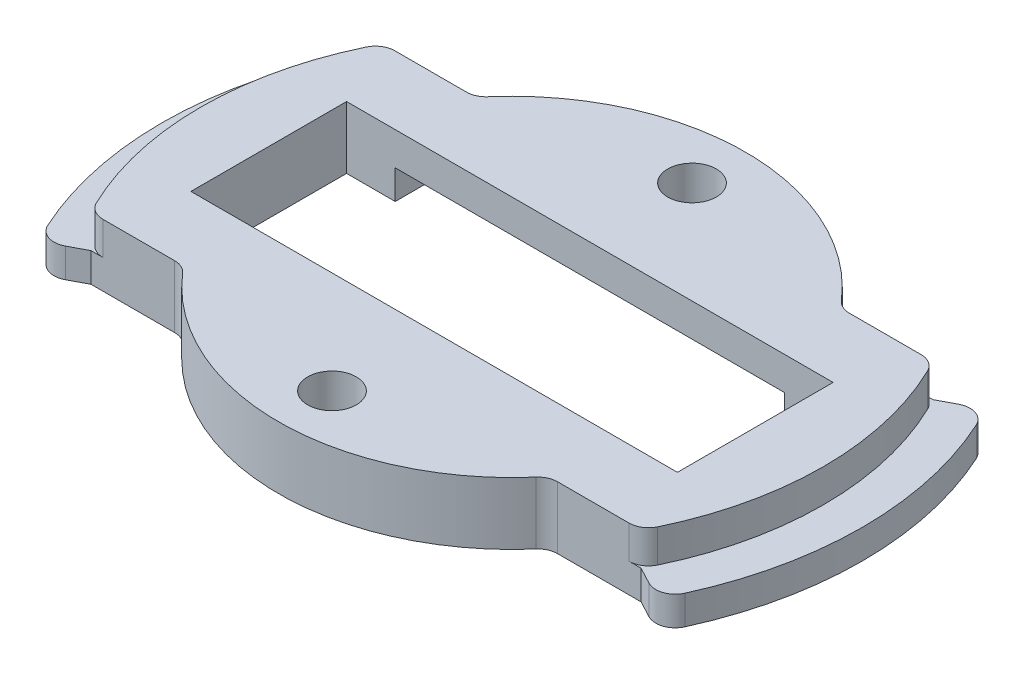
SolidWorks part; units mm, degrees
material "ABS"
ref_plane "Front Plane" through (0, 0, 0) normal (0, 0, 1) x (1, 0, 0)
ref_plane "Top Plane" through (0, 0, 0) normal (0, 1, 0) x (1, 0, 0)
ref_plane "Right Plane" through (0, 0, 0) normal (1, 0, 0) x (0, 0, -1)
sketch "Sketch1" plane through (0, 0, 0) normal (0, 1, 0) x (1, 0, 0)
  line L0 (0, 0) -> (0, 8) construction
  line L1 (0, 0) -> (20, 0) construction
  line L2 (-20, 8) -> (20, 8)
  line L3 (-20, 8) -> (-20, -8)
  line L4 (-20, -8) -> (20, -8)
  line L5 (20, 8) -> (20, -8)
  line L6 (28.2666, 15) -> (-28.2666, 15)
  line L7 (28.2666, -15) -> (-28.2666, -15)
  line L8 (-25, 15) -> (-25, -15) construction
  line L9 (-28.2666, 15) -> (-28.2666, -15) construction
  arc A0 (-28.2666, 15) -> (-28.2666, -15) centre (0, 0) ccw
  arc A1 (28.2666, 15) -> (28.2666, -15) centre (0, 0) cw
  point P10 (0, 15)
  point P17 (0, -15)
  dimension "D4" = 5
  dimension "D5" = 32
  dimension "D1" = 40
  dimension "D2" = 16
  dimension "D3" = 15
extrude "Boss-Extrude1" add sketch "Sketch1" along normal blind 6.4
sketch "Sketch2" plane through (0, 0, 0) normal (0, -1, 0) x (1, 0, 0)
  line L0 (-20, 0) -> (20, 0) construction
  line L1 (-20, 8) -> (20, 8)
  line L2 (-20, 8) -> (-20, 12)
  line L3 (-20, 12) -> (20, 12)
  line L4 (20, 8) -> (20, 12)
  line L5 (-20, -8) -> (-20, 8) construction
  line L6 (20, 8) -> (20, -8) construction
  line L7 (20, -8) -> (20, -12)
  line L8 (-20, -12) -> (20, -12)
  line L9 (-20, -8) -> (-20, -12)
  line L10 (-20, -8) -> (20, -8)
  dimension "D1" = 4
extrude "Cut-Extrude1" cut sketch "Sketch2" against normal blind 3
sketch "Sketch3" plane through (0, 0, 0) normal (0, -1, 0) x (1, 0, 0)
  line L0 (0, 12) -> (0, -12) construction
  line L1 (20, 12) -> (-20, 12) construction
  line L2 (-20, -12) -> (20, -12) construction
  line L3 (-20, -12) -> (-20, 12) construction
  line L4 (-20, 8) -> (-25, 8)
  line L5 (-20, 8) -> (-20, -8)
  line L6 (-20, -8) -> (-25, -8)
  line L7 (-25, 8) -> (-25, -8)
  line L8 (-20, 8) -> (20, 8) construction
  line L9 (20, -8) -> (-20, -8) construction
  line L10 (25, 8) -> (25, -8)
  line L11 (20, -8) -> (25, -8)
  line L12 (20, 8) -> (20, -8)
  line L13 (20, 8) -> (25, 8)
  dimension "D1" = 5
extrude "Cut-Extrude2" cut sketch "Sketch3" against normal through all
sketch "Sketch5" plane through (0, 6.4, 0) normal (0, 1, 0) x (1, 0, 0)
  line L0 (-28.2666, -15) -> (28.2666, -15) construction
  line L1 (-18.735, -15) -> (18.735, -15)
  line L2 (-25, 0) -> (25, 0) construction
  line L3 (-25, -8) -> (-25, 8) construction
  line L4 (25, 8) -> (25, -8) construction
  line L5 (-18.735, 15) -> (18.735, 15)
  arc A0 (-18.735, -15) -> (18.735, -15) centre (0, 0) ccw
  arc A1 (-18.735, 15) -> (18.735, 15) centre (0, 0) cw
  dimension "D1" = 24
extrude "Boss-Extrude2" add sketch "Sketch5" against normal up to surface (6.4 mm away) up to face at (0, 0, 0)
sketch "Sketch6" plane through (0, 0, 0) normal (0, -1, 0) x (1, 0, 0)
  line L0 (-28.2666, 15) -> (0, 0) construction
  line L1 (0, 0) -> (-28.2666, -15) construction
  line L2 (0, 0) -> (0, 24) construction
  line L3 (-31.7999, -16.875) -> (-28.2666, -15)
  line L4 (-31.7999, 16.875) -> (-28.2666, 15)
  line L5 (31.7999, -16.875) -> (28.2666, -15)
  line L6 (31.7999, 16.875) -> (28.2666, 15)
  arc A0 (-28.2666, 15) -> (-28.2666, -15) centre (0, 0) ccw construction
  arc A1 (28.2666, -15) -> (28.2666, 15) centre (0, 0) ccw construction
  arc A2 (-28.2666, 15) -> (-28.2666, -15) centre (0, 0) ccw
  arc A3 (28.2666, -15) -> (28.2666, 15) centre (0, 0) ccw
  arc A4 (18.735, 15) -> (-18.735, 15) centre (0, 0) ccw construction
  arc A5 (-31.7999, 16.875) -> (-31.7999, -16.875) centre (0, 0) ccw
  arc A6 (28.2666, 15) -> (28.2666, -15) centre (0, 0) cw
  arc A7 (31.7999, 16.875) -> (31.7999, -16.875) centre (0, 0) cw
  arc M13 (28.2666, -15) -> (28.2666, 15) centre (0, 0) ccw
  arc M17 (-28.2666, 15) -> (-28.2666, -15) centre (0, 0) ccw
  dimension "D1" = 4
extrude "Boss-Extrude3" add sketch "Sketch6" against normal blind 3 contours L4 A5 L3 M17 | A7 L6 L5 M13
fillet "Fillet1" radius 2 12 edges at (-18.735, 3.2, 15) (18.735, 3.2, 15) (18.735, 3.2, -15) (-18.735, 3.2, -15) (-28.2666, 4.7, -15) (-28.2666, 4.7, 15) (28.2666, 4.7, 15) (28.2666, 4.7, -15) (31.7999, 1.5, -16.875) (31.7999, 1.5, 16.875) (-31.7999, 1.5, 16.875) (-31.7999, 1.5, -16.875)
sketch "Sketch7" plane through (0, 6.4, 0) normal (0, 1, 0) x (1, 0, 0)
  line L0 (-25, 0) -> (25, 0) construction
  line L1 (-25, -8) -> (-25, 8) construction
  line L2 (25, 8) -> (25, -8) construction
  line L3 (0, 24) -> (0, -24) construction
  arc A0 (18.1591, 15.6923) -> (-18.1591, 15.6923) centre (0, 0) ccw construction
  arc A1 (-18.1591, -15.6923) -> (18.1591, -15.6923) centre (0, 0) ccw construction
  circle A2 centre (0, 18.5) radius 2.5
  circle A3 centre (0, 18.5) radius 5.5 construction
  circle A4 centre (0, -18.5) radius 2.5
  dimension "D1" = 3
  dimension "D2" = 5
extrude "Cut-Extrude3" cut sketch "Sketch7" against normal through all
